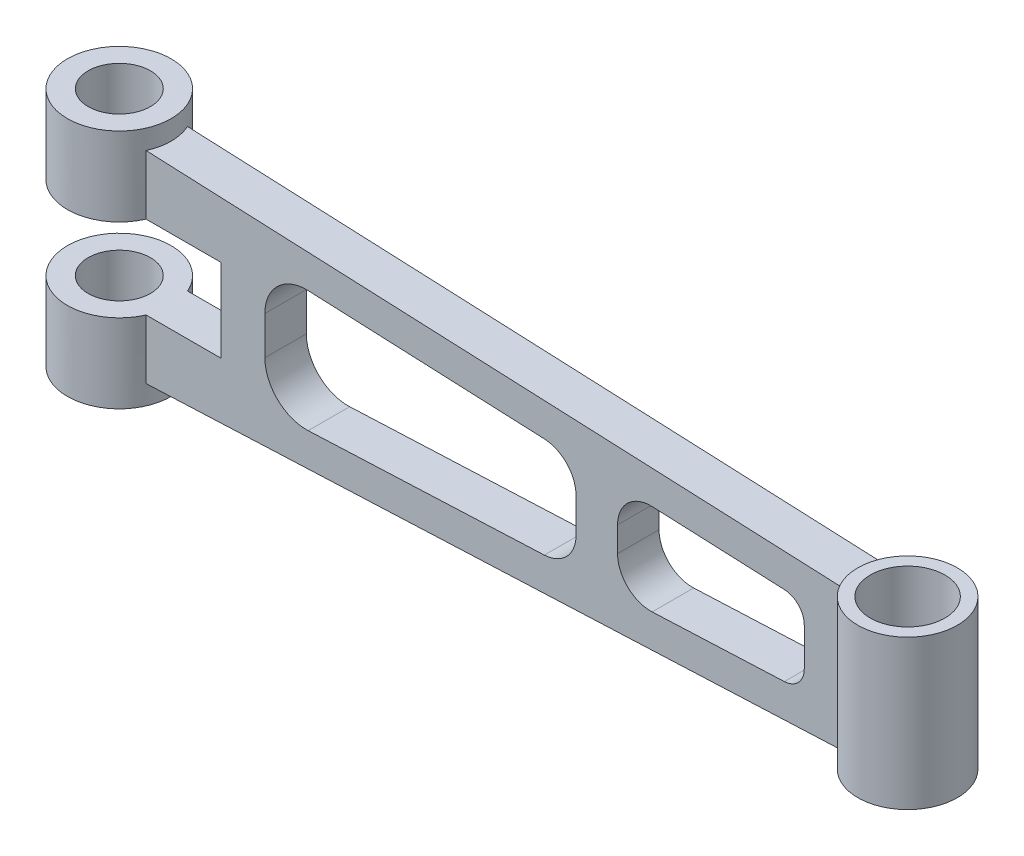
SolidWorks part; units mm, degrees
ref_plane "Front Plane" through (0, 0, 0) normal (0, 0, 1) x (1, 0, 0)
ref_plane "Top Plane" through (0, 0, 0) normal (0, 1, 0) x (1, 0, 0)
ref_plane "Right Plane" through (0, 0, 0) normal (1, 0, 0) x (0, 0, -1)
sketch "Sketch1" plane through (0, 0, 0) normal (0, 1, 0) x (1, 0, 0)
  line L0 (0, 0) -> (190, 0) construction
  line L2 (11.4564, 5) -> (179.0913, 5)
  line L3 (11.4564, 5) -> (11.4564, -5)
  line L4 (11.4564, -5) -> (179.0913, -5)
  line L5 (179.0913, 5) -> (179.0913, -5)
  circle A0 centre (0, 0) radius 12.5
  circle A1 centre (190, 0) radius 12
  circle A2 centre (0, 0) radius 7.5
  circle A3 centre (190, 0) radius 9
  dimension "D1" = 25
  dimension "D2" = 24
  dimension "D5" = 18
  dimension "D6" = 15
  dimension "D3" = 190
  dimension "D4" = 10
extrude "Boss-Extrude1" add sketch "Sketch1" along normal blind 58
sketch "Sketch2" plane through (0, 0, -5) normal (0, 0, -1) x (-1, 0, 0)
  line L0 (12.5, 29) -> (-202, 29) construction
  line L1 (12.5, 0) -> (12.5, 58) construction
  line L2 (-202, 58) -> (-202, 0) construction
  line L3 (-179.0913, 58) -> (-179.0913, 0) construction
  line L4 (-179.0913, 11) -> (-202, 11)
  line L5 (-179.0913, 11) -> (-179.0913, 47)
  line L6 (-179.0913, 47) -> (-202, 47)
  line L7 (-202, 11) -> (-202, 47)
  line L8 (-179.0913, 11) -> (-202, 47) construction
  line L9 (-179.0913, 47) -> (-202, 11) construction
  line L10 (12.5, 29) -> (-11.4564, 29) construction
  line L11 (-11.4564, 58) -> (-11.4564, 0) construction
  line L12 (-11.4564, 29) -> (0.5218, 29) construction
  line L13 (0.5218, 29) -> (0.5218, 22.1145) construction
  line L14 (-150.5456, 47.255) -> (-150.5456, 10.745) construction
  line L15 (-11.4564, 19) -> (12.5, 19)
  line L16 (-11.4564, 19) -> (-11.4564, 39)
  line L17 (-11.4564, 39) -> (12.5, 39)
  line L18 (12.5, 19) -> (12.5, 39)
  line L19 (-11.4564, 19) -> (12.5, 39) construction
  line L20 (-11.4564, 39) -> (12.5, 19) construction
  line L21 (-170.0913, 19.606) -> (-170.0913, 38.394)
  line L22 (-170.0913, 38.394) -> (-125.0913, 40.3587)
  line L23 (-125.0913, 40.3587) -> (-125.0913, 17.6413)
  line L24 (-179.0913, 46.0087) -> (-11.4564, 53.3278)
  line L25 (-11.4564, 58) -> (12.5, 58)
  line L26 (-11.4564, 58) -> (-11.4564, 0)
  line L27 (-11.4564, 0) -> (12.5, 0)
  line L28 (12.5, 58) -> (12.5, 0)
  line L29 (-11.4564, 39) -> (-29.5, 39)
  line L30 (-11.4564, 39) -> (-11.4564, 19)
  line L31 (-11.4564, 19) -> (-29.5, 19)
  line L32 (-29.5, 39) -> (-29.5, 19)
  line L33 (-179.0913, 11.9913) -> (-11.4564, 4.6722)
  line L34 (-115.0913, 17.2047) -> (-115.0913, 40.7953)
  line L35 (-115.0913, 40.7953) -> (-40.0913, 44.0699)
  line L36 (-40.0913, 44.0699) -> (-40.0913, 13.9301)
  line L37 (-115.0913, 17.2047) -> (-40.0913, 13.9301)
  line L38 (-170.0913, 19.606) -> (-125.0913, 17.6413)
  line L39 (-11.4564, 0) -> (12.5, 0) construction
  line L40 (-202, 58) -> (12.5, 58)
  line L41 (-202, 58) -> (-202, 0)
  line L42 (-202, 0) -> (12.5, 0)
  line L43 (12.5, 58) -> (12.5, 0)
  line L44 (-11.4564, 0) -> (12.5, 0)
  point P6 (-190.5456, 29)
  point P46 (-40.0913, 29)
  point P47 (-115.0913, 29)
  point P48 (-125.0913, 29)
  point P49 (-170.0913, 29)
  line M3 (-179.0913, 0) -> (-11.4564, 0)
  line M4 (-11.4564, 0) -> (-11.4564, 58)
  line M5 (-11.4564, 58) -> (-179.0913, 58)
  line M6 (-179.0913, 58) -> (-179.0913, 0)
  dimension "D1" = 36
  dimension "D2" = 20
  dimension "D3" = 42
  dimension "D4" = 5
  dimension "D5" = 40
  dimension "D6" = 36.51
  dimension "D7" = 8
  dimension "D8" = 8
  dimension "D9" = 45
  dimension "D10" = 75
  dimension "D11" = 9
  dimension "D12" = 10
extrude "Cut-Extrude1" cut sketch "Sketch2" against normal through all both and the other way through all contours L40 L41 L6 M6 | L24 M6 M4 M5 | L41 L42 L4 M6 | L33 M6 M3 M4 | L21 L38 L23 L22 | L34 L37 L36 L35 | L29 L32 L31 M4 | L15 L18 L17 M4
sketch "Sketch3" plane through (0, 11, 0) normal (0, -1, 0) x (1, 0, 0)
  line L1 (179.0913, 5) -> (179.0913, -5)
  line L2 (179.0913, 5) -> (179.0913, -5)
  circle A0 centre (190, 0) radius 12
  arc A1 (179.0913, -5) -> (179.0913, 5) centre (190, 0) ccw
  arc A2 (179.0913, -5) -> (179.0913, 5) centre (190, 0) ccw
  line M4 (179.0913, 5) -> (179.0913, -5)
  dimension "D1" = 0
extrude "Boss-Extrude2" add sketch "Sketch3" against normal up to next contours A0 M4
sketch "Sketch4" plane through (0, 0, 0) normal (0, -1, 0) x (1, 0, 0)
  line L1 (11.4564, -5) -> (11.4564, 5)
  line L2 (11.4564, -5) -> (11.4564, 5)
  circle A0 centre (0, 0) radius 12.5
  arc A1 (11.4564, 5) -> (11.4564, -5) centre (0, 0) ccw
  arc A2 (11.4564, 5) -> (11.4564, -5) centre (0, 0) ccw
  line M4 (11.4564, -5) -> (11.4564, 5)
  dimension "D1" = 0
extrude "Boss-Extrude3" add sketch "Sketch4" against normal up to next contours A0 M4
ref_plane "Plane1" through (0, 29, 0) normal (0, -1, 0) x (-1, 0, 0)
mirror "Mirror1" about plane through (0, 29, 0) normal (0, -1, 0) of "Boss-Extrude2", "Boss-Extrude3"
fillet "Fillet1" radius 5 2 edges at (170.0913, 19.606, 0) (170.0913, 38.394, 0)
fillet "Fillet2" radius 8 4 edges at (115.0913, 40.7953, 0) (115.0913, 17.2047, 0) (125.0913, 17.6413, 0) (125.0913, 40.3587, 0)
fillet "Fillet3" radius 10 2 edges at (40.0913, 13.9301, 0) (40.0913, 44.0699, 0)
